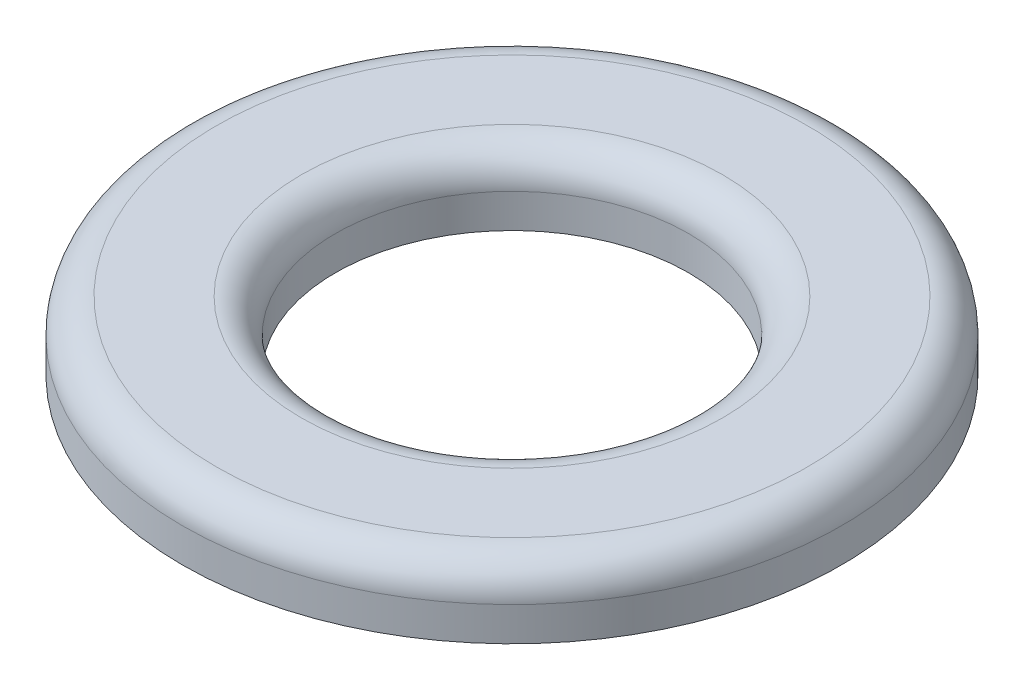
SolidWorks part; units mm, degrees
material "普通碳钢"
ref_plane "前视基准面" through (0, 0, 0) normal (0, 0, 1) x (1, 0, 0)
ref_plane "上视基准面" through (0, 0, 0) normal (0, 1, 0) x (1, 0, 0)
ref_plane "右视基准面" through (0, 0, 0) normal (1, 0, 0) x (0, 0, -1)
sketch "草图1" plane through (0, 0, 0) normal (0, 1, 0) x (1, 0, 0)
  circle A0 centre (0, 0) radius 4.85
  circle A1 centre (0, 0) radius 2.6
  dimension "D1" = 9.7
  dimension "D2" = 5.2
extrude "凸台-拉伸1" add sketch "草图1" along normal blind 1
fillet "圆角1" radius 0.5 2 edges at (0, 1, 2.6) (0, 1, 4.85)
